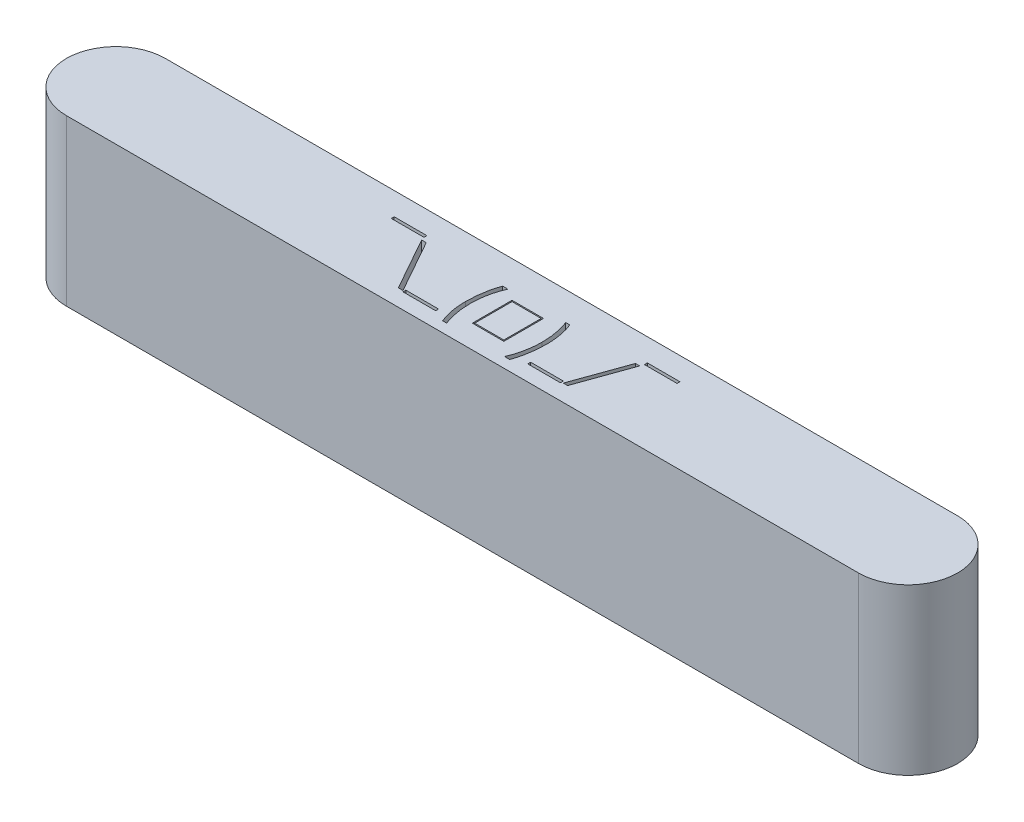
SolidWorks part; units mm, degrees
ref_plane "Front Plane" through (0, 0, 0) normal (0, 0, 1) x (1, 0, 0)
ref_plane "Top Plane" through (0, 0, 0) normal (0, 1, 0) x (1, 0, 0)
ref_plane "Right Plane" through (0, 0, 0) normal (1, 0, 0) x (0, 0, -1)
sketch "Sketch1" plane through (0, 0, 0) normal (0, 1, 0) x (1, 0, 0)
  line L3 (-30.48, 3.81) -> (30.48, 3.81)
  line L4 (-30.48, -3.81) -> (30.48, -3.81)
  arc A2 (30.48, -3.81) -> (30.48, 3.81) centre (30.48, 0) ccw
  arc A3 (-30.48, 3.81) -> (-30.48, -3.81) centre (-30.48, 0) ccw
  point P2 (0, 0)
  point P8 (-31.75, 0)
  point P9 (31.75, 0)
  dimension "D1" = 63.5
extrude "Boss-Extrude1" add sketch "Sketch1" along normal blind 12.7
sketch "Sketch2" plane through (0, 0, 0) normal (0, -1, 0) x (1, 0, 0)
  line L0 (-30.988, 0) -> (30.988, 0) construction
  line L1 (-30.988, 1.397) -> (30.988, 1.397)
  line L2 (-30.988, -1.397) -> (30.988, -1.397)
  arc A0 (-30.988, 1.397) -> (-30.988, -1.397) centre (-30.988, 0) ccw
  arc A1 (30.988, -1.397) -> (30.988, 1.397) centre (30.988, 0) ccw
  point P2 (0, 0)
  point P8 (-32.385, 0)
  point P9 (32.385, 0)
  dimension "D1" = 1.397
  dimension "D2" = 64.77
extrude "Cut-Extrude1" cut sketch "Sketch2" against normal blind 10.16
sketch "Sketch3" plane through (0, 12.7, 0) normal (0, 1, 0) x (1, 0, 0)
  text T0 "¯\\_(ツ)_/¯"
  point P1 (-8.5345, -0.6738)
  point P2 (-12.3526, -1.4973)
  point P3 (-10.0318, -1.123)
  point P4 (0, 0)
  point P5 (-11.4542, -0.9732)
  point P6 (0, 0)
  point P7 (-11.0799, -2.0213)
  point P8 (0, 0)
  point P9 (0, 0)
extrude "Cut-Extrude2" cut sketch "Sketch3" against normal blind 1.27
